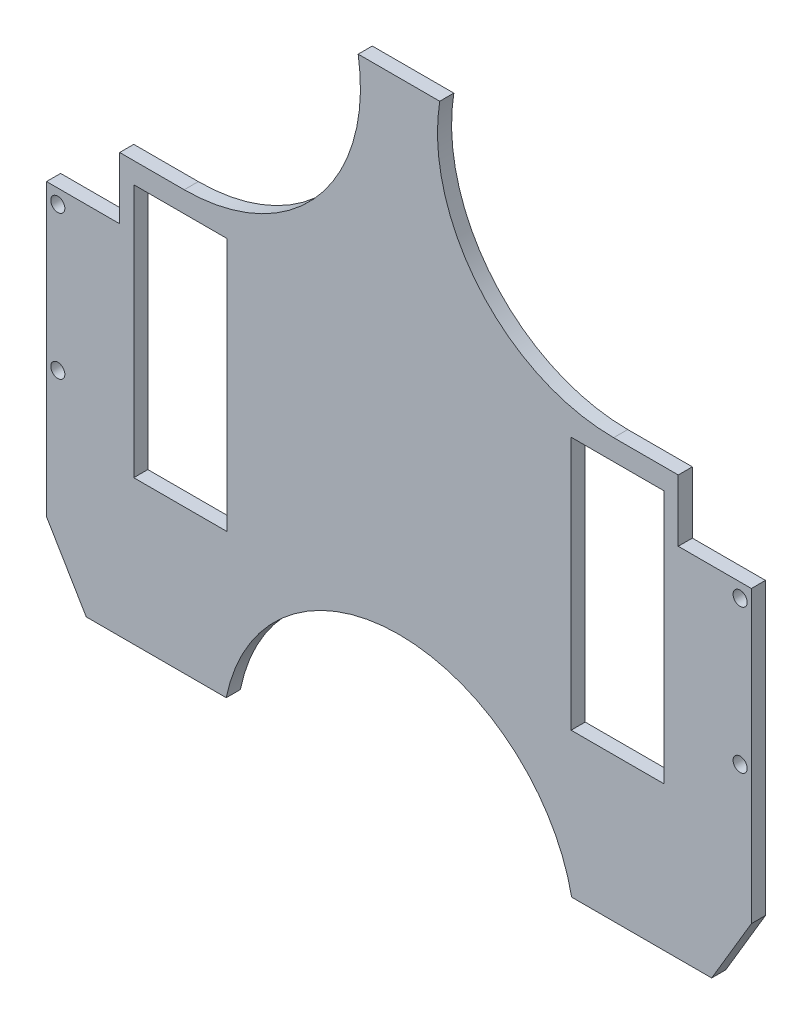
SolidWorks part; units mm, degrees
ref_plane "Front Plane" through (0, 0, 0) normal (0, 0, 1) x (1, 0, 0)
ref_plane "Top Plane" through (0, 0, 0) normal (0, 1, 0) x (1, 0, 0)
ref_plane "Right Plane" through (0, 0, 0) normal (1, 0, 0) x (0, 0, -1)
sketch "Sketch1" plane through (0, 0, 0) normal (0, 0, 1) x (1, 0, 0)
  line L0 (-3462.1019, -146.8192) -> (-3462.1019, -236.8192)
  line L13 (-3306.9819, -146.8192) -> (-3306.9819, -236.8192)
  line L14 (-3462.1019, -146.8192) -> (-3429.1019, -146.8192)
  line L15 (-3273.9819, -236.8192) -> (-3306.9819, -236.8192)
  line L21 (-3273.9819, -146.8192) -> (-3306.9819, -146.8192)
  line L25 (-3273.9819, -146.8192) -> (-3273.9819, -236.8192)
  line L42 (-3462.1019, -236.8192) -> (-3429.1019, -236.8192)
  line L43 (-3429.1019, -146.8192) -> (-3429.1019, -236.8192)
  line L44 (-3429.1019, -146.8192) -> (-3462.1019, -146.8192) construction
  line L45 (-3462.1019, -146.8192) -> (-3462.1019, -236.8192) construction
  line L48 (-3429.1019, -236.8192) -> (-3429.1019, -146.8192) construction
  line L52 (-3462.1019, -236.8192) -> (-3429.1019, -236.8192) construction
  line L62 (-3368.0419, -66.9192) -> (-3368.0419, -288.0048) construction
  line L68 (-3493.0419, -66.9192) -> (-3243.0419, -66.9192)
  line L78 (-3493.0419, -66.9192) -> (-3493.0419, -288.0048)
  line L79 (-3243.0419, -66.9192) -> (-3243.0419, -288.0048)
  line L80 (-3493.0419, -288.0048) -> (-3243.0419, -288.0048)
  line L83 (-3493.0419, -161.3192) -> (-3493.0419, -259.0407) construction
  line L87 (-3353.5801, -66.9192) -> (-3382.5038, -66.9192) construction
  line L90 (-3243.0419, -259.0407) -> (-3243.0419, -161.3192) construction
  circle A6 centre (-3489.0419, -217.3192) radius 2.5
  circle A7 centre (-3489.0419, -166.3192) radius 2.5
  circle A14 centre (-3489.0419, -217.3192) radius 2.1 construction
  circle A15 centre (-3489.0419, -166.3192) radius 2.5 construction
  circle A16 centre (-3489.0419, -217.3192) radius 2.5 construction
  circle A17 centre (-3247.0419, -166.3192) radius 2.5
  circle A18 centre (-3247.0419, -217.3192) radius 2.5
extrude "Boss-Extrude1" add sketch "Sketch1" along normal blind 5
ref_plane "Plane1"
sketch "Sketch6" plane through (0, 0, 0) normal (0, 0, 1) x (1, 0, 0)
  line L13 (-3503.4579, -270.4515) -> (-3493.0419, -264.2708)
  line L19 (-3493.0419, -161.3192) -> (-3493.0419, -66.9192)
  line L25 (-3503.4579, -270.4515) -> (-3489.3744, -294.1855)
  line L29 (-3493.0419, -161.3192) -> (-3467.1019, -161.3192)
  line L30 (-3493.0419, -66.9192) -> (-3382.5038, -66.9192)
  line L31 (-3467.1019, -161.3192) -> (-3467.1019, -139.4192)
  line L33 (-3493.0419, -264.2708) -> (-3478.9585, -288.0048)
  line L37 (-3493.0419, -161.3192) -> (-3467.1019, -161.3192) construction
  line L38 (-3353.5801, -66.9192) -> (-3382.5038, -66.9192) construction
  line L40 (-3467.1019, -161.3192) -> (-3467.1019, -139.4192) construction
  line L41 (-3493.0419, -161.3192) -> (-3493.0419, -259.0407) construction
  line L43 (-3467.1019, -139.4192) -> (-3444.1986, -139.4192)
  line L44 (-3467.1019, -139.4192) -> (-3445.0038, -139.4192) construction
  line L45 (-3489.3744, -294.1855) -> (-3478.9585, -288.0048)
  line L47 (-3493.0419, -66.9192) -> (-3493.0419, -288.0048) construction
  line L48 (-3493.0419, -288.0048) -> (-3243.0419, -288.0048) construction
  line L49 (-3368.0419, -66.9192) -> (-3368.0419, -288.0048) construction
  line L50 (-3243.0419, -66.9192) -> (-3493.0419, -66.9192) construction
  line L51 (-3246.7095, -294.1855) -> (-3257.1254, -288.0048)
  line L52 (-3268.9819, -139.4192) -> (-3291.8853, -139.4192)
  line L53 (-3243.0419, -264.2708) -> (-3257.1254, -288.0048)
  line L54 (-3268.9819, -161.3192) -> (-3268.9819, -139.4192)
  line L55 (-3243.0419, -66.9192) -> (-3353.5801, -66.9192)
  line L56 (-3243.0419, -161.3192) -> (-3268.9819, -161.3192)
  line L57 (-3232.626, -270.4515) -> (-3246.7095, -294.1855)
  line L58 (-3243.0419, -161.3192) -> (-3243.0419, -66.9192)
  line L59 (-3232.626, -270.4515) -> (-3243.0419, -264.2708)
  arc A1 (-3444.1986, -139.4192) -> (-3382.5038, -66.9192) centre (-3444.1986, -76.9192) ccw
  arc A2 (-3291.8853, -139.4192) -> (-3353.5801, -66.9192) centre (-3291.8853, -76.9192) cw
  circle A3 centre (-3368.0419, -300.4173) radius 62.5
  arc A4 (-3305.5419, -300.4173) -> (-3430.5419, -300.4173) centre (-3368.0419, -300.4173) ccw construction
  dimension "D1" = 62.5
extrude "Cut-Extrude4" cut sketch "Sketch6" along normal through all
